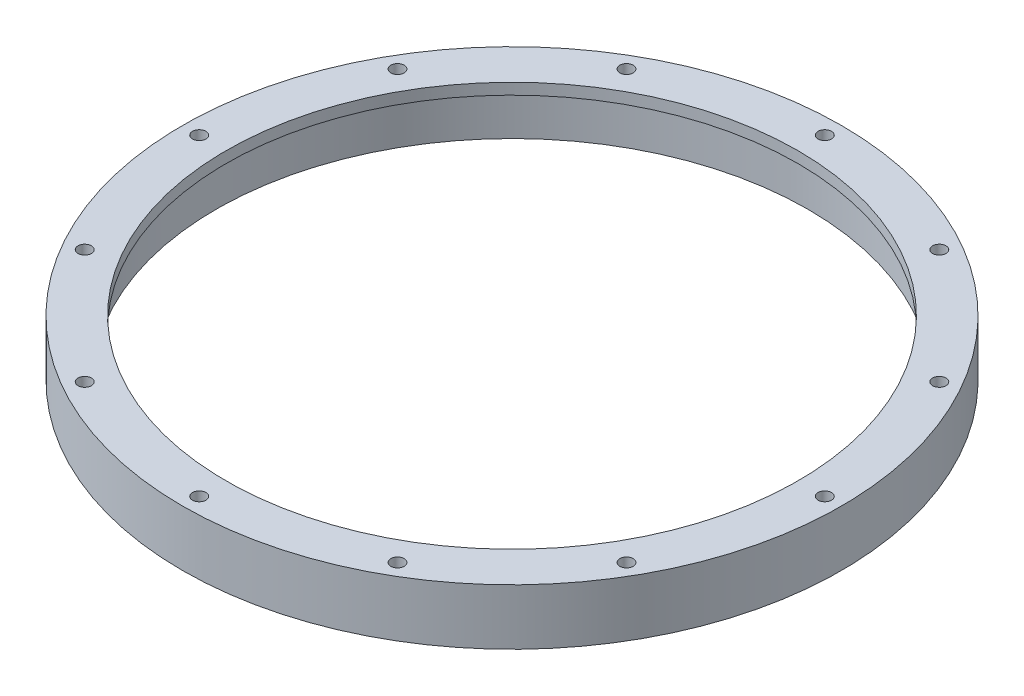
SolidWorks part; units mm, degrees
material "6061-T6 (SS)"
ref_plane "前视基准面" through (0, 0, 0) normal (0, 0, 1) x (1, 0, 0)
ref_plane "上视基准面" through (0, 0, 0) normal (0, 1, 0) x (1, 0, 0)
ref_plane "右视基准面" through (0, 0, 0) normal (1, 0, 0) x (0, 0, -1)
sketch "草图1" plane through (0, 0, 0) normal (0, 0, 1) x (1, 0, 0)
  line L0 (0, 0) -> (0, 34.9743) construction
  line L1 (-53, 0) -> (-59, 0)
  line L2 (-59, 0) -> (-59, 10)
  line L3 (-59, 10) -> (-51.2, 10)
  line L4 (-51.2, 10) -> (-51.2, 8)
  line L5 (-51.2, 8) -> (-53, 8)
  line L6 (-53, 8) -> (-53, 0)
  dimension "D1" = 106
  dimension "D2" = 2
  dimension "D3" = 1.8
  dimension "D4" = 8
  dimension "D5" = 6
revolve "旋转1" add sketch "草图1" angle 360 about L0
sketch "草图2" plane through (0, 0, 0) normal (0, -1, 0) x (1, 0, 0)
  circle A0 centre (0, 0) radius 56 construction
  circle A1 centre (0, 0) radius 53 construction
  circle A2 centre (0, 56) radius 1.2
  dimension "D1" = 3
  dimension "D2" = 2.4
extrude "切除-拉伸1" cut sketch "草图2" against normal blind 10
cosmetic thread "装饰螺纹线1" parameters "D2"=3
pattern_circular "阵列(圆周)1" count 12 over 360 about axis through (0, 0, 0) along (0, 1, 0) of "切除-拉伸1"
